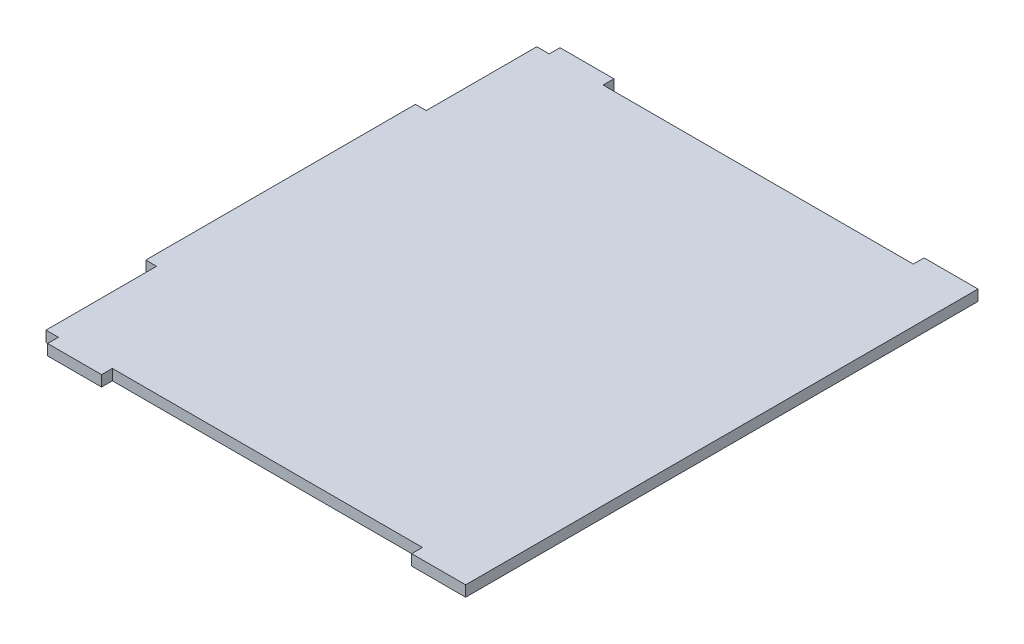
SolidWorks part; units mm, degrees
ref_plane "Front Plane" through (0, 0, 0) normal (0, 0, 1) x (1, 0, 0)
ref_plane "Top Plane" through (0, 0, 0) normal (0, 1, 0) x (1, 0, 0)
ref_plane "Right Plane" through (0, 0, 0) normal (1, 0, 0) x (0, 0, -1)
sketch "Sketch1" plane through (0, 0, 0) normal (0, 1, 0) x (1, 0, 0)
  line L0 (-77.805, -91) -> (-73.1993, -91)
  line L8 (-53.1993, -95) -> (-73.1993, -95)
  line L9 (-73.1993, -91) -> (-73.1993, -95)
  line L11 (-53.1993, -95) -> (-53.1993, -91)
  line L14 (81.8007, -95) -> (81.8007, -94.995)
  line L16 (-77.805, -91) -> (-77.805, -50)
  line L17 (0, 0) -> (-134.6142, 0) construction
  line L18 (-77.805, 50) -> (-81.805, 50)
  line L19 (-81.805, -50) -> (-81.805, 50)
  line L20 (-81.805, -50) -> (-77.805, -50)
  line L21 (-77.805, 50) -> (-77.805, 91)
  line L22 (-53.1993, -91) -> (61.8007, -91)
  line L23 (61.8007, -95) -> (81.805, -95)
  line L24 (81.805, 95) -> (81.805, -95)
  line L25 (-77.805, 91) -> (-73.1993, 91)
  line L26 (-53.1993, 91) -> (61.8007, 91)
  line L27 (61.8007, 91) -> (61.8007, 95)
  line L28 (-53.1993, 95) -> (-53.1993, 91)
  line L29 (-73.1993, 91) -> (-73.1993, 95)
  line L30 (-73.1993, 95) -> (-53.1993, 95)
  line L31 (61.8007, 95) -> (81.805, 95)
  line L32 (61.8007, -91) -> (61.8007, -95)
  line L33 (81.8007, -94.995) -> (81.805, -95) construction
  point P0 (0, 0)
  dimension "D1" = 115
  dimension "D2" = 20.0043
  dimension "D3" = 100
  dimension "D4" = 50
  dimension "D5" = 20
extrude "Boss-Extrude1" add sketch "Sketch1" along normal blind 4 contours L24 L23 L32 L22 L11 L8 L9 L0 L16 L20 L19 L18 L21 L25 L29 L30 L28 L26 L27 L31
